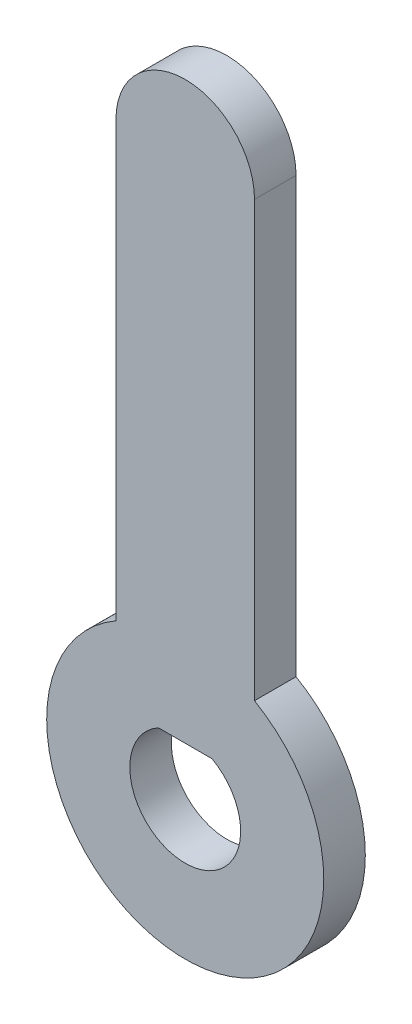
SolidWorks part; units mm, degrees
ref_plane "Plan de face" through (0, 0, 0) normal (0, 0, 1) x (1, 0, 0)
ref_plane "Plan de dessus" through (0, 0, 0) normal (0, 1, 0) x (1, 0, 0)
ref_plane "Plan de droite" through (0, 0, 0) normal (1, 0, 0) x (0, 0, -1)
sketch "Esquisse1" plane through (0, 0, 0) normal (0, 0, 1) x (1, 0, 0)
  line L0 (0, 0) -> (0, 40) construction
  line L1 (-5, 8.6603) -> (-5, 40)
  line L2 (5, 8.6603) -> (5, 40)
  line L3 (-5, 40) -> (5, 40) construction
  line L4 (-5, 8.6603) -> (5, 8.6603) construction
  arc A0 (-5, 8.6603) -> (5, 8.6603) centre (0, 0) ccw
  arc A2 (5, 40) -> (-5, 40) centre (0, 40) ccw
  point P5 (0, 40)
  dimension "D2" = 20
  dimension "D3" = 10
  dimension "D1" = 40
  dimension "D4" = 10
extrude "Extrusion1" add sketch "Esquisse1" along normal blind 3
sketch "Esquisse2" plane through (0, 0, 3) normal (0, 0, 1) x (1, 0, 0)
  line L0 (-1.9365, 3.5) -> (1.9365, 3.5)
  arc A0 (-1.9365, 3.5) -> (1.9365, 3.5) centre (0, 0) ccw
  dimension "D1" = 8
  dimension "D2" = 3.5
extrude "Extrusion2" cut sketch "Esquisse2" against normal through all
